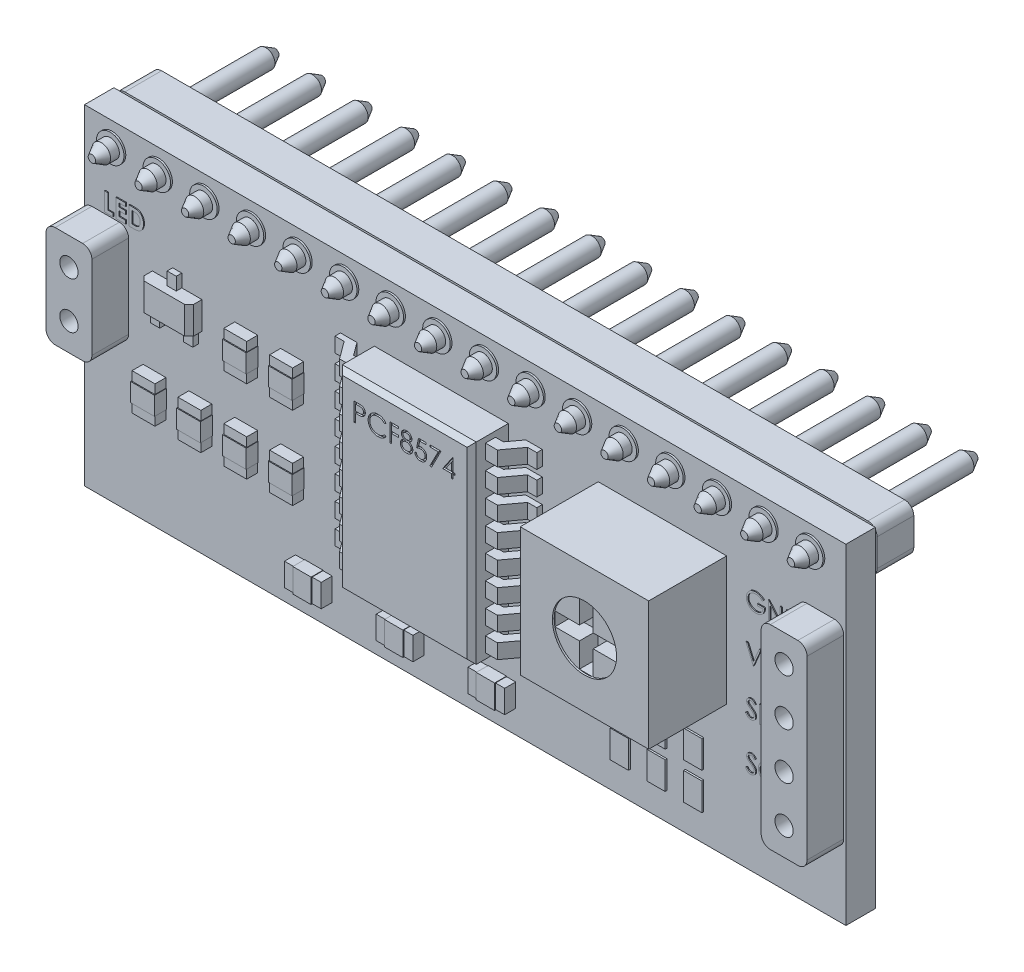
SolidWorks part; units mm, degrees
ref_plane "Front Plane" through (0, 0, 0) normal (0, 0, 1) x (1, 0, 0)
ref_plane "Top Plane" through (0, 0, 0) normal (0, 1, 0) x (1, 0, 0)
ref_plane "Right Plane" through (0, 0, 0) normal (1, 0, 0) x (0, 0, -1)
sketch "Sketch1" plane through (0, 0, 0) normal (0, 0, 1) x (1, 0, 0)
  line L1 (-20.75, 9) -> (20.75, 9)
  line L2 (-20.75, 9) -> (-20.75, -9)
  line L3 (-20.75, -9) -> (20.75, -9)
  line L4 (20.75, 9) -> (20.75, -9)
  line L5 (-20.75, 9) -> (20.75, -9) construction
  line L6 (-20.75, -9) -> (20.75, 9) construction
  point P0 (0, 0)
  dimension "D1" = 18
  dimension "D2" = 41.5
extrude "Boss-Extrude1" add sketch "Sketch1" along normal blind 1.6
sketch "Sketch2" plane through (0, 0, 1.6) normal (0, 0, 1) x (1, 0, 0)
  line L0 (20.75, 9) -> (-20.75, 9) construction
  line L1 (-20.75, 9) -> (-20.75, -9) construction
  circle A0 centre (-19.25, 7.75) radius 0.75
  dimension "D3" = 1.5
  dimension "D1" = 1.25
  dimension "D2" = 1.5
extrude "Boss-Extrude2" add sketch "Sketch2" along normal blind 0.1 and the other way blind 1.7
pattern_linear "LPattern1" count 16 spacing 2.54 along (1, 0, 0) of "Boss-Extrude2"
sketch "Sketch3" plane through (0, 0, 1.7) normal (0, 0, 1) x (1, 0, 0)
  line L2 (20.75, 9) -> (-20.75, 9) construction
  circle A0 centre (-19.25, 7.75) radius 0.5
  circle A1 centre (-16.7091, 7.75) radius 0.5
  circle A2 centre (-14.1682, 7.75) radius 0.5
  circle A3 centre (-11.6273, 7.75) radius 0.5
  circle A4 centre (-9.0864, 7.75) radius 0.5
  circle A5 centre (-6.5455, 7.75) radius 0.5
  circle A6 centre (-4.0045, 7.75) radius 0.5
  circle A7 centre (-1.4636, 7.75) radius 0.5
  circle A8 centre (1.0773, 7.75) radius 0.5
  circle A9 centre (3.6182, 7.75) radius 0.5
  circle A10 centre (6.1591, 7.75) radius 0.5
  circle A11 centre (8.7, 7.75) radius 0.5
  circle A12 centre (11.2409, 7.75) radius 0.5
  circle A13 centre (13.7818, 7.75) radius 0.5
  circle A14 centre (16.3227, 7.75) radius 0.5
  circle A15 centre (18.8636, 7.75) radius 0.5
  dimension "D1" = 1
  dimension "D3" = 1.25
  dimension "D2" = 16
extrude "Cut-Extrude1" cut sketch "Sketch3" against normal blind 1.8
sketch "Sketch4" plane through (0, 0, 1.6) normal (0, 0, 1) x (1, 0, 0)
  line L0 (20.75, 9) -> (-20.75, 9) construction
  line L1 (-4.95, 5.5) -> (2.35, 5.5)
  line L2 (-4.95, 5.5) -> (-4.95, -5)
  line L3 (-4.95, -5) -> (2.35, -5)
  line L4 (2.35, 5.5) -> (2.35, -5)
  line L5 (-20.75, 9) -> (-20.75, -9) construction
  dimension "D1" = 10.5
  dimension "D2" = 7.3
  dimension "D3" = 3.5
  dimension "D4" = 15.8
extrude "Boss-Extrude4" add sketch "Sketch4" along normal blind 2
sketch "Sketch5" plane through (0, 0, 1.6) normal (0, 0, 1) x (1, 0, 0)
  line L0 (-1.3, 5.5) -> (-1.3, -5) construction
  line L1 (2.35, 5.5) -> (-4.95, 5.5) construction
  line L2 (-4.95, -5) -> (2.35, -5) construction
  line L3 (-6.8, 3.1) -> (4.2, 3.1)
  line L4 (-6.8, 5.2) -> (4.2, 5.2)
  line L5 (-6.8, 5.2) -> (-6.8, 4.4)
  line L6 (-6.8, 4.4) -> (4.2, 4.4)
  line L7 (4.2, 5.2) -> (4.2, 4.4)
  line L8 (-6.8, 3.9) -> (-6.8, 3.1)
  line L9 (-6.8, 3.9) -> (4.2, 3.9)
  line L10 (4.2, 3.9) -> (4.2, 3.1)
  line L11 (-6.8, 1.8) -> (4.2, 1.8)
  line L12 (-6.8, 2.6) -> (-6.8, 1.8)
  line L13 (-6.8, 2.6) -> (4.2, 2.6)
  line L14 (4.2, 2.6) -> (4.2, 1.8)
  line L15 (-6.8, 0.5) -> (4.2, 0.5)
  line L16 (-6.8, 1.3) -> (-6.8, 0.5)
  line L17 (-6.8, 1.3) -> (4.2, 1.3)
  line L18 (4.2, 1.3) -> (4.2, 0.5)
  line L19 (-6.8, -0.8) -> (4.2, -0.8)
  line L20 (-6.8, 0) -> (-6.8, -0.8)
  line L21 (-6.8, 0) -> (4.2, 0)
  line L22 (4.2, 0) -> (4.2, -0.8)
  line L23 (-6.8, -2.1) -> (4.2, -2.1)
  line L24 (-6.8, -1.3) -> (-6.8, -2.1)
  line L25 (-6.8, -1.3) -> (4.2, -1.3)
  line L26 (4.2, -1.3) -> (4.2, -2.1)
  line L27 (-6.8, -3.4) -> (4.2, -3.4)
  line L28 (-6.8, -2.6) -> (-6.8, -3.4)
  line L29 (-6.8, -2.6) -> (4.2, -2.6)
  line L30 (4.2, -2.6) -> (4.2, -3.4)
  line L31 (-6.8, -4.7) -> (4.2, -4.7)
  line L32 (-6.8, -3.9) -> (-6.8, -4.7)
  line L33 (-6.8, -3.9) -> (4.2, -3.9)
  line L34 (4.2, -3.9) -> (4.2, -4.7)
  dimension "D1" = 11
  dimension "D2" = 5.5
  dimension "D3" = 0.3
  dimension "D4" = 0.8
  dimension "D5" = 8
extrude "Boss-Extrude6" add sketch "Sketch5" along normal blind 1.25
sketch "Sketch6" plane through (0, -4.7, 0) normal (0, -1, 0) x (1, 0, 0)
  line L0 (-6.8, 1.9) -> (-6.3, 1.9)
  line L1 (-6.8, 2.85) -> (-6.8, 1.6) construction
  line L2 (-6.3, 1.9) -> (-5.6, 2.85)
  line L3 (-6.8, 2.85) -> (-4.95, 2.85) construction
  line L4 (-5.6, 2.85) -> (-6.8, 2.85)
  line L5 (-6.8, 2.85) -> (-6.8, 1.9)
  line L6 (-4.95, 1.6) -> (-5.9, 1.6)
  line L7 (-6.8, 1.6) -> (-4.95, 1.6) construction
  line L8 (-5.9, 1.6) -> (-5.3842, 2.3)
  line L9 (-5.3842, 2.3) -> (-4.95, 2.3)
  line L10 (-4.95, 1.6) -> (-4.95, 2.85) construction
  line L11 (-4.95, 2.3) -> (-4.95, 1.6)
  line L12 (-1.3, 3.6) -> (-1.3, 1.6) construction
  line L13 (-4.95, 3.6) -> (2.35, 3.6) construction
  line L14 (-4.95, 1.6) -> (2.35, 1.6) construction
  line L15 (2.7842, 2.3) -> (2.35, 2.3)
  line L16 (2.35, 2.3) -> (2.35, 1.6)
  line L17 (2.35, 1.6) -> (3.3, 1.6)
  line L18 (3.3, 1.6) -> (2.7842, 2.3)
  line L19 (4.2, 1.9) -> (3.7, 1.9)
  line L20 (4.2, 2.85) -> (4.2, 1.9)
  line L21 (3, 2.85) -> (4.2, 2.85)
  line L22 (3.7, 1.9) -> (3, 2.85)
  dimension "D1" = 0.5
  dimension "D2" = 0.5
  dimension "D3" = 0.3
  dimension "D4" = 0.7
  dimension "D5" = 1.2
  dimension "D6" = 0.5
extrude "Cut-Extrude3" cut sketch "Sketch6" against normal blind 10
sketch "Sketch7" plane through (0, 0, 1.6) normal (0, 0, 1) x (1, 0, 0)
  line L0 (20.75, -9) -> (20.75, 9) construction
  line L2 (20.75, 9) -> (-20.75, 9) construction
  circle A0 centre (19.48, 3.75) radius 0.75
  circle A2 centre (19.48, 1.21) radius 0.75
  circle A3 centre (19.48, -1.33) radius 0.75
  circle A4 centre (19.48, -3.87) radius 0.75
  dimension "D1" = 1.5
  dimension "D2" = 1.27
  dimension "D3" = 5.25
  dimension "D4" = 4
extrude "Boss-Extrude8" add sketch "Sketch7" along normal blind 0.1 and the other way blind 1.7
sketch "Sketch8" plane through (0, 0, 1.7) normal (0, 0, 1) x (1, 0, 0)
  circle A0 centre (19.48, 3.75) radius 0.5
  circle A1 centre (19.48, 1.21) radius 0.5
  circle A2 centre (19.48, -1.33) radius 0.5
  circle A3 centre (19.48, -3.87) radius 0.5
  dimension "D1" = 1
  dimension "D2" = 4
extrude "Cut-Extrude4" cut sketch "Sketch8" against normal blind 1.8
chamfer "Chamfer1" distance 0.25 angle 45 4 edges at (2.35, 0.25, 3.6) (-4.95, 0.25, 3.6) (-1.3, 5.5, 3.6) (-1.3, -5, 3.6)
sketch "Sketch9" plane through (0, 0, 1.6) normal (0, 0, 1) x (1, 0, 0)
  line L0 (20.75, 9) -> (-20.75, 9) construction
  line L1 (-20.75, 9) -> (-20.75, -9) construction
  circle A0 centre (-19.5, 3) radius 0.75
  circle A1 centre (-19.5, 0.46) radius 0.75
  dimension "D1" = 1.5
  dimension "D2" = 1.5
  dimension "D3" = 2.54
  dimension "D4" = 6
  dimension "D5" = 1.25
  dimension "D6" = 1.25
extrude "Boss-Extrude9" add sketch "Sketch9" along normal blind 0.1 and the other way blind 1.7
sketch "Sketch10" plane through (0, 0, 1.7) normal (0, 0, 1) x (1, 0, 0)
  circle A0 centre (-19.5, 3) radius 0.5
  circle A1 centre (-19.5, 0.46) radius 0.5
  dimension "D1" = 1
  dimension "D2" = 1
extrude "Cut-Extrude5" cut sketch "Sketch10" against normal blind 1.8
sketch "Sketch11" plane through (0, 0, 1.6) normal (0, 0, 1) x (1, 0, 0)
  line L0 (20.75, -9) -> (20.75, 9) construction
  line L1 (7.25, 5.2) -> (14.25, 5.2)
  line L2 (7.25, 5.2) -> (7.25, -1.8)
  line L3 (7.25, -1.8) -> (14.25, -1.8)
  line L4 (14.25, 5.2) -> (14.25, -1.8)
  line L5 (20.75, 9) -> (-20.75, 9) construction
  dimension "D1" = 7
  dimension "D2" = 7
  dimension "D3" = 6.5
  dimension "D4" = 3.8
extrude "Boss-Extrude10" add sketch "Sketch11" along normal blind 4.25
sketch "Sketch12" plane through (0, 0, 5.85) normal (0, 0, 1) x (1, 0, 0)
  line L0 (7.25, 5.2) -> (7.25, -1.8) construction
  line L1 (14.25, 5.2) -> (7.25, 5.2) construction
  circle A0 centre (10.75, 1.7) radius 1.75
  point P4 (10.75, 5.2)
  dimension "D3" = 3.5
  dimension "D1" = 3.5
  dimension "D2" = 3.5
extrude "Cut-Extrude6" cut sketch "Sketch12" against normal blind 0.1
sketch "Sketch13" plane through (0, 0, 5.75) normal (0, 0, 1) x (1, 0, 0)
  line L0 (10.375, 1.325) -> (10.375, -0.0093)
  line L1 (10.375, 3.4093) -> (11.125, 3.4093)
  line L2 (10.375, 3.4093) -> (10.375, 2.075)
  line L3 (10.375, -0.0093) -> (11.125, -0.0093)
  line L4 (11.125, 3.4093) -> (11.125, 2.075)
  line L7 (9.0407, 2.075) -> (10.375, 2.075)
  line L8 (9.0407, 2.075) -> (9.0407, 1.325)
  line L9 (9.0407, 1.325) -> (10.375, 1.325)
  line L10 (12.4593, 2.075) -> (12.4593, 1.325)
  line L15 (11.125, 1.325) -> (11.125, -0.0093)
  line L16 (11.125, 2.075) -> (12.4593, 2.075)
  line L17 (11.125, 1.325) -> (12.4593, 1.325)
  circle A0 centre (10.75, 1.7) radius 1.75 construction
  point P0 (10.75, 1.7)
  point P8 (10.75, 1.7)
  dimension "D1" = 0.75
  dimension "D2" = 0.75
extrude "Cut-Extrude7" cut sketch "Sketch13" against normal blind 1
sketch "Sketch14" plane through (0, 0, 1.6) normal (0, 0, 1) x (1, 0, 0)
  line L0 (20.75, -9) -> (20.75, 9) construction
  line L1 (2.75, -6.5) -> (0.75, -6.5)
  line L2 (2.75, -6.5) -> (2.75, -7.75)
  line L3 (2.75, -7.75) -> (0.75, -7.75)
  line L4 (0.75, -6.5) -> (0.75, -7.75)
  line L5 (-2.25, -6.5) -> (-4.25, -6.5)
  line L6 (-2.25, -6.5) -> (-2.25, -7.75)
  line L7 (-2.25, -7.75) -> (-4.25, -7.75)
  line L8 (-4.25, -6.5) -> (-4.25, -7.75)
  line L9 (-7.25, -6.5) -> (-9.25, -6.5)
  line L10 (-7.25, -6.5) -> (-7.25, -7.75)
  line L11 (-7.25, -7.75) -> (-9.25, -7.75)
  line L12 (-9.25, -6.5) -> (-9.25, -7.75)
  line L13 (-20.75, -9) -> (20.75, -9) construction
  dimension "D1" = 2
  dimension "D2" = 1.25
  dimension "D3" = 2
  dimension "D4" = 2
  dimension "D5" = 3
  dimension "D6" = 3
  dimension "D7" = 18
  dimension "D8" = 1.25
  dimension "D9" = 1.25
  dimension "D10" = 1.25
  dimension "D11" = 1.25
  dimension "D12" = 1.25
extrude "Boss-Extrude11" add sketch "Sketch14" along normal blind 0.6
sketch "Sketch15" plane through (0, 0, 1.6) normal (0, 0, 1) x (1, 0, 0)
  line L0 (-12.5607, -3.6613) -> (-12.5607, -1.6613)
  line L1 (-8.8107, -3.6613) -> (-10.0607, -3.6613)
  line L2 (-8.8107, -3.6613) -> (-8.8107, -1.6613)
  line L3 (-8.8107, -1.6613) -> (-10.0607, -1.6613)
  line L4 (-10.0607, -3.6613) -> (-10.0607, -1.6613)
  line L5 (-11.3107, -3.6613) -> (-12.5607, -3.6613)
  line L6 (-11.3107, -3.6613) -> (-11.3107, -1.6613)
  line L7 (-11.3107, -1.6613) -> (-12.5607, -1.6613)
  line L8 (-15.0607, -3.6613) -> (-15.0607, -1.6613)
  line L9 (-13.8107, -3.6613) -> (-15.0607, -3.6613)
  line L10 (-13.8107, -3.6613) -> (-13.8107, -1.6613)
  line L11 (-13.8107, -1.6613) -> (-15.0607, -1.6613)
  line L12 (-17.5607, -3.6613) -> (-17.5607, -1.6613)
  line L13 (-16.3107, -3.6613) -> (-17.5607, -3.6613)
  line L14 (-16.3107, -3.6613) -> (-16.3107, -1.6613)
  line L15 (-16.3107, -1.6613) -> (-17.5607, -1.6613)
  dimension "D1" = 2
  dimension "D2" = 1.25
  dimension "D3" = 4
extrude "Boss-Extrude12" add sketch "Sketch15" along normal blind 0.6
sketch "Sketch16" plane through (0, 0, 1.6) normal (0, 0, 1) x (1, 0, 0)
  line L0 (-8.8107, -1.6613) -> (-10.0607, -1.6613) construction
  line L1 (-8.8107, 0.8387) -> (-10.0607, 0.8387)
  line L2 (-8.8107, 0.8387) -> (-8.8107, 2.8387)
  line L3 (-8.8107, 2.8387) -> (-10.0607, 2.8387)
  line L4 (-10.0607, 0.8387) -> (-10.0607, 2.8387)
  line L5 (-12.5607, 0.8387) -> (-12.5607, 2.8387)
  line L6 (-11.3107, 2.8387) -> (-12.5607, 2.8387)
  line L7 (-11.3107, 0.8387) -> (-11.3107, 2.8387)
  line L8 (-11.3107, 0.8387) -> (-12.5607, 0.8387)
  dimension "D1" = 2.5
  dimension "D3" = 1.25
  dimension "D4" = 0
  dimension "D5" = 2
  dimension "D2" = 2
extrude "Boss-Extrude13" add sketch "Sketch16" along normal blind 0.6
sketch "Sketch17" plane through (0, 0, 1.6) normal (0, 0, 1) x (1, 0, 0)
  line L0 (-20.75, -9) -> (20.75, -9) construction
  line L1 (8, -7.5) -> (9, -7.5)
  line L2 (8, -7.5) -> (8, -6)
  line L3 (8, -6) -> (9, -6)
  line L4 (9, -7.5) -> (9, -6)
  line L5 (8, -5.5) -> (9, -5.5)
  line L6 (8, -5.5) -> (8, -4)
  line L7 (8, -4) -> (9, -4)
  line L8 (9, -5.5) -> (9, -4)
  line L9 (20.75, -9) -> (20.75, 9) construction
  line L10 (10, -5.5) -> (10, -4)
  line L11 (10, -4) -> (11, -4)
  line L12 (11, -5.5) -> (11, -4)
  line L13 (10, -5.5) -> (11, -5.5)
  line L14 (10, -6) -> (11, -6)
  line L15 (11, -7.5) -> (11, -6)
  line L16 (10, -7.5) -> (10, -6)
  line L17 (10, -7.5) -> (11, -7.5)
  line L18 (12, -5.5) -> (12, -4)
  line L19 (12, -4) -> (13, -4)
  line L20 (13, -5.5) -> (13, -4)
  line L21 (12, -5.5) -> (13, -5.5)
  line L22 (12, -6) -> (13, -6)
  line L23 (13, -7.5) -> (13, -6)
  line L24 (12, -7.5) -> (12, -6)
  line L25 (12, -7.5) -> (13, -7.5)
  dimension "D1" = 1
  dimension "D2" = 1
  dimension "D3" = 0.5
  dimension "D4" = 1.5
  dimension "D5" = 1.5
  dimension "D6" = 1.5
  dimension "D7" = 12.75
  dimension "D8" = 3
extrude "Boss-Extrude14" add sketch "Sketch17" along normal blind 0.1
sketch "Sketch19" plane through (0, 0, 2.2) normal (0, 0, 1) x (1, 0, 0)
  line L0 (-9.25, -7.75) -> (-7.25, -7.75) construction
  line L1 (-8.75, -6.475) -> (-7.75, -6.475)
  line L2 (-8.75, -6.475) -> (-8.75, -7.775)
  line L3 (-8.75, -7.775) -> (-7.75, -7.775)
  line L4 (-7.75, -6.475) -> (-7.75, -7.775)
  line L5 (-8.75, -6.475) -> (-7.75, -7.775) construction
  line L6 (-8.75, -7.775) -> (-7.75, -6.475) construction
  line L7 (-9.25, -6.5) -> (-9.25, -7.75) construction
  line L8 (-3.75, -6.475) -> (-3.75, -7.775)
  line L9 (-3.75, -6.475) -> (-2.75, -6.475)
  line L10 (-2.75, -6.475) -> (-2.75, -7.775)
  line L11 (-3.75, -7.775) -> (-2.75, -7.775)
  line L12 (1.25, -6.475) -> (1.25, -7.775)
  line L13 (1.25, -6.475) -> (2.25, -6.475)
  line L14 (2.25, -6.475) -> (2.25, -7.775)
  line L15 (1.25, -7.775) -> (2.25, -7.775)
  point P0 (-8.25, -7.125)
  dimension "D1" = 1.3
  dimension "D2" = 0.025
  dimension "D3" = 1
  dimension "D4" = 0.5
  dimension "D5" = 3
extrude "Boss-Extrude16" add sketch "Sketch19" against normal blind 0.6 and the other way blind 0.05
sketch "Sketch20" plane through (0, 0, 2.2) normal (0, 0, 1) x (1, 0, 0)
  line L0 (-17.5607, -1.6613) -> (-17.5607, -3.6613) construction
  line L1 (-17.5857, -2.1613) -> (-16.2857, -2.1613)
  line L2 (-17.5857, -2.1613) -> (-17.5857, -3.1613)
  line L3 (-17.5857, -3.1613) -> (-16.2857, -3.1613)
  line L4 (-16.2857, -2.1613) -> (-16.2857, -3.1613)
  line L5 (-17.5857, -2.1613) -> (-16.2857, -3.1613) construction
  line L6 (-17.5857, -3.1613) -> (-16.2857, -2.1613) construction
  line L7 (-17.5607, -3.6613) -> (-16.3107, -3.6613) construction
  line L8 (-15.0857, -2.1613) -> (-13.7857, -2.1613)
  line L9 (-15.0857, -2.1613) -> (-15.0857, -3.1613)
  line L10 (-13.7857, -2.1613) -> (-13.7857, -3.1613)
  line L11 (-15.0857, -3.1613) -> (-13.7857, -3.1613)
  line L12 (-12.5857, -2.1613) -> (-11.2857, -2.1613)
  line L13 (-12.5857, -2.1613) -> (-12.5857, -3.1613)
  line L14 (-11.2857, -2.1613) -> (-11.2857, -3.1613)
  line L15 (-12.5857, -3.1613) -> (-11.2857, -3.1613)
  line L16 (-10.0857, -2.1613) -> (-8.7857, -2.1613)
  line L17 (-10.0857, -2.1613) -> (-10.0857, -3.1613)
  line L18 (-8.7857, -2.1613) -> (-8.7857, -3.1613)
  line L19 (-10.0857, -3.1613) -> (-8.7857, -3.1613)
  point P0 (-16.9357, -2.6613)
  dimension "D1" = 0.025
  dimension "D2" = 1.3
  dimension "D3" = 1
  dimension "D4" = 0.5
  dimension "D5" = 4
extrude "Boss-Extrude17" add sketch "Sketch20" against normal blind 0.6 and the other way blind 0.05
sketch "Sketch21" plane through (0, 0, 2.2) normal (0, 0, 1) x (1, 0, 0)
  line L0 (-12.5607, 2.8387) -> (-12.5607, 0.8387) construction
  line L1 (-12.5857, 2.3387) -> (-11.2857, 2.3387)
  line L2 (-12.5857, 2.3387) -> (-12.5857, 1.3387)
  line L3 (-12.5857, 1.3387) -> (-11.2857, 1.3387)
  line L4 (-11.2857, 2.3387) -> (-11.2857, 1.3387)
  line L5 (-12.5857, 2.3387) -> (-11.2857, 1.3387) construction
  line L6 (-12.5857, 1.3387) -> (-11.2857, 2.3387) construction
  line L7 (-12.5607, 0.8387) -> (-11.3107, 0.8387) construction
  line L8 (-10.0857, 2.3387) -> (-8.7857, 2.3387)
  line L9 (-10.0857, 2.3387) -> (-10.0857, 1.3387)
  line L10 (-8.7857, 2.3387) -> (-8.7857, 1.3387)
  line L11 (-10.0857, 1.3387) -> (-8.7857, 1.3387)
  point P0 (-11.9357, 1.8387)
  dimension "D1" = 1.3
  dimension "D2" = 0.025
  dimension "D3" = 0.5
  dimension "D4" = 1
  dimension "D5" = 2
extrude "Boss-Extrude18" add sketch "Sketch21" against normal blind 0.6 and the other way blind 0.05
sketch "Sketch23" plane through (0, 0, 1.6) normal (0, 0, 1) x (1, 0, 0)
  line L0 (-20.75, 9) -> (-20.75, -9) construction
  line L1 (-17.05, 3) -> (-14.35, 3)
  line L2 (-17.05, 3) -> (-17.05, 1.5)
  line L3 (-17.05, 1.5) -> (-14.35, 1.5)
  line L4 (-14.35, 3) -> (-14.35, 1.5)
  line L5 (-17.05, 3) -> (-14.35, 1.5) construction
  line L6 (-17.05, 1.5) -> (-14.35, 3) construction
  line L7 (20.75, 9) -> (-20.75, 9) construction
  point P0 (-15.7, 2.25)
  dimension "D1" = 2.7
  dimension "D2" = 1.5
  dimension "D3" = 3.7
  dimension "D4" = 6
extrude "Boss-Extrude19" add sketch "Sketch23" along normal blind 0.7
sketch "Sketch24" plane through (0, 0, 1.6) normal (0, 0, 1) x (1, 0, 0)
  line L0 (-14.35, 3) -> (-17.05, 3) construction
  line L1 (-15.95, 3) -> (-15.45, 3)
  line L2 (-15.95, 3) -> (-15.95, 3.7)
  line L3 (-15.95, 3.7) -> (-15.45, 3.7)
  line L4 (-15.45, 3) -> (-15.45, 3.7)
  line L5 (-17.05, 1.5) -> (-14.35, 1.5) construction
  line L6 (-16.85, 1.5) -> (-16.35, 1.5)
  line L7 (-16.85, 1.5) -> (-16.85, 0.8)
  line L8 (-16.85, 0.8) -> (-16.35, 0.8)
  line L9 (-16.35, 1.5) -> (-16.35, 0.8)
  line L10 (-17.05, 1.5) -> (-14.35, 1.5) construction
  line L11 (-14.55, 1.5) -> (-15.05, 1.5)
  line L12 (-14.55, 1.5) -> (-14.55, 0.8)
  line L13 (-14.55, 0.8) -> (-15.05, 0.8)
  line L14 (-15.05, 1.5) -> (-15.05, 0.8)
  line L15 (-17.05, 3) -> (-17.05, 1.5) construction
  line L16 (-14.35, 1.5) -> (-14.35, 3) construction
  dimension "D1" = 0.5
  dimension "D2" = 1.1
  dimension "D3" = 0.2
  dimension "D4" = 0.2
  dimension "D5" = 0.5
  dimension "D6" = 0.5
  dimension "D7" = 0.7
  dimension "D8" = 0.7
  dimension "D9" = 0.7
extrude "Boss-Extrude20" add sketch "Sketch24" along normal blind 0.3
chamfer "Chamfer2" distance 0.25 angle 45 2 edges at (-14.35, 2.25, 2.3) (-17.05, 2.25, 2.3)
sketch "Sketch25" plane through (0, 0, 1.7) normal (0, 0, 1) x (1, 0, 0)
  circle A0 centre (-19.25, 7.75) radius 0.5
  circle A1 centre (-16.71, 7.75) radius 0.5
  circle A2 centre (-14.17, 7.75) radius 0.5
  circle A3 centre (-11.63, 7.75) radius 0.5
  circle A4 centre (-9.09, 7.75) radius 0.5
  circle A5 centre (-6.55, 7.75) radius 0.5
  circle A6 centre (-4.01, 7.75) radius 0.5
  circle A7 centre (-1.47, 7.75) radius 0.5
  circle A8 centre (1.07, 7.75) radius 0.5
  circle A9 centre (3.61, 7.75) radius 0.5
  circle A10 centre (6.15, 7.75) radius 0.5
  circle A11 centre (8.69, 7.75) radius 0.5
  circle A12 centre (11.23, 7.75) radius 0.5
  circle A13 centre (13.77, 7.75) radius 0.5
  circle A14 centre (16.31, 7.75) radius 0.5
  circle A15 centre (18.85, 7.75) radius 0.5
  dimension "D1" = 16
extrude "Boss-Extrude21" add sketch "Sketch25" along normal blind 1 and the other way blind 9
sketch "Sketch27" plane through (0, 0, -0.1) normal (0, 0, -1) x (-1, 0, 0)
  line L0 (20.75, 9) -> (20.75, -9) construction
  line L1 (-20.75, 9) -> (20.75, 9)
  line L2 (-20.75, 9) -> (-20.75, 6.5)
  line L3 (-20.75, 6.5) -> (20.75, 6.5)
  line L4 (20.75, 9) -> (20.75, 6.5)
  dimension "D1" = 2.5
extrude "Boss-Extrude23" add sketch "Sketch27" along normal blind 2
fillet "Fillet3" radius 0.5 4 edges at (-20.75, 6.5, -1.1) (-20.75, 9, -1.1) (20.75, 6.5, -1.1) (20.75, 9, -1.1)
sketch "Sketch28" plane through (0, 0, 1.6) normal (0, 0, 1) x (1, 0, 0)
  text T0 "<b>LED</b>" font "Century Gothic" height 1
extrude "Boss-Extrude24" add sketch "Sketch28" along normal blind 0.05
sketch "Sketch29" plane through (0, 0, 1.6) normal (0, 0, 1) x (1, 0, 0)
  text T0 "GND\r\nVCC\r\nSDA\r\nSCL" font "Century Gothic" height 0.95
extrude "Boss-Extrude25" add sketch "Sketch29" along normal blind 0.05
sketch "Sketch30" plane through (0, 0, 3.6) normal (0, 0, 1) x (1, 0, 0)
  text T0 "PCF8574" font "Century Gothic" height 1
extrude "Cut-Extrude8" cut sketch "Sketch30" against normal blind 0.1
sketch "Sketch31" plane through (0, 0, 1.7) normal (0, 0, 1) x (1, 0, 0)
  line L1 (-20.75, 4.5) -> (-18.25, 4.5)
  line L2 (-20.75, 4.5) -> (-20.75, -1.04)
  line L3 (-20.75, -1.04) -> (-18.25, -1.04)
  line L4 (-18.25, 4.5) -> (-18.25, -1.04)
  line L5 (18.23, 5.25) -> (20.73, 5.25)
  line L6 (18.23, 5.25) -> (18.23, -5.37)
  line L7 (18.23, -5.37) -> (20.73, -5.37)
  line L8 (20.73, 5.25) -> (20.73, -5.37)
  circle A0 centre (-19.5, 3) radius 0.5 construction
  circle A1 centre (-19.5, 0.46) radius 0.5 construction
  circle A2 centre (19.48, 1.21) radius 0.5 construction
  circle A3 centre (19.48, 3.75) radius 0.5 construction
  circle A4 centre (19.48, -3.87) radius 0.5 construction
  dimension "D6" = 1.25
  dimension "D7" = 1.5
  dimension "D1" = 1.5
  dimension "D2" = 2.5
  dimension "D3" = 1.25
  dimension "D4" = 1.5
  dimension "D5" = 2.5
  dimension "D8" = 1.5
extrude "Boss-Extrude26" add sketch "Sketch31" along normal blind 2
fillet "Fillet4" radius 0.5 8 edges at (18.23, 5.25, 2.7) (20.73, 5.25, 2.7) (18.23, -5.37, 2.7) (20.73, -5.37, 2.7) (-18.25, 4.5, 2.7) (-20.75, 4.5, 2.7) (-18.25, -1.04, 2.7) (-20.75, -1.04, 2.7)
sketch "Sketch32" plane through (0, 0, 1.7) normal (0, 0, -1) x (-1, 0, 0)
  circle A0 centre (-19.48, 3.75) radius 0.5
  circle A1 centre (-19.48, 1.21) radius 0.5
  circle A2 centre (-19.48, -1.33) radius 0.5
  circle A3 centre (-19.48, -3.87) radius 0.5
  circle A4 centre (19.5, 3) radius 0.5
  circle A5 centre (19.5, 0.46) radius 0.5
extrude "Cut-Extrude9" cut sketch "Sketch32" against normal blind 2
chamfer "Chamfer3" distance 0.3 angle 60 32 edges at (-16.21, 7.75, 2.7) (19.35, 7.75, 2.7) (16.81, 7.75, 2.7) (14.27, 7.75, 2.7) (11.73, 7.75, 2.7) (9.19, 7.75, 2.7) (6.65, 7.75, 2.7) (4.11, 7.75, 2.7) (1.57, 7.75, 2.7) (-0.97, 7.75, 2.7) (-3.51, 7.75, 2.7) (-6.05, 7.75, 2.7) (-8.59, 7.75, 2.7) (-11.13, 7.75, 2.7) (-13.67, 7.75, 2.7) (-18.75, 7.75, 2.7) (-18.75, 7.75, -7.3) (-16.21, 7.75, -7.3) (-13.67, 7.75, -7.3) (-11.13, 7.75, -7.3) (-8.59, 7.75, -7.3) (-6.05, 7.75, -7.3) (-3.51, 7.75, -7.3) (-0.97, 7.75, -7.3) (1.57, 7.75, -7.3) (4.11, 7.75, -7.3) (6.65, 7.75, -7.3) (9.19, 7.75, -7.3) (11.73, 7.75, -7.3) (14.27, 7.75, -7.3) (16.81, 7.75, -7.3) (19.35, 7.75, -7.3)
